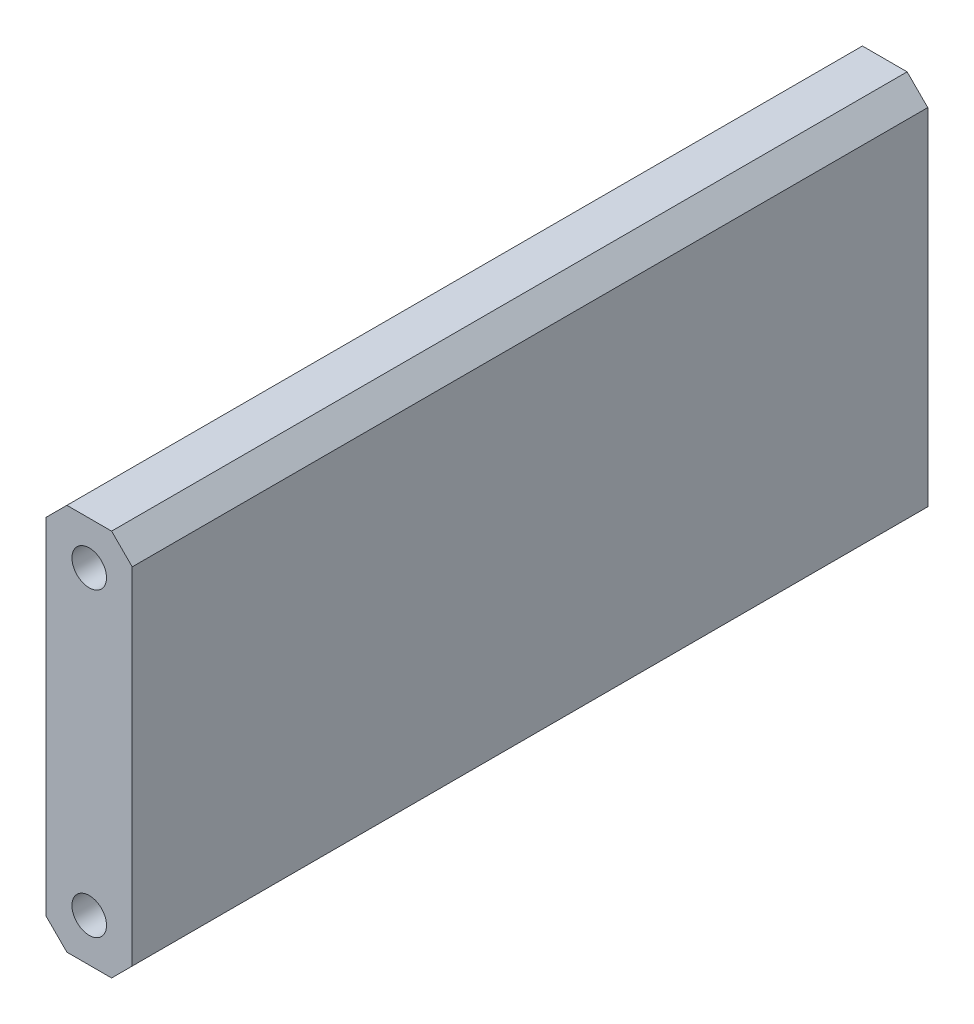
SolidWorks part; units mm, degrees
material "304 SSTL"
ref_plane "Front" through (0, 0, 0) normal (0, 0, 1) x (1, 0, 0)
ref_plane "Top" through (0, 0, 0) normal (0, 1, 0) x (1, 0, 0)
ref_plane "Right" through (0, 0, 0) normal (1, 0, 0) x (0, 0, -1)
sketch "Sketch1" plane through (0, 0, 0) normal (0, 0, 1) x (1, 0, 0)
  line L0 (0, 0) -> (0, -44.45) construction
  line L1 (-3.302, 6.35) -> (-6.35, 3.302)
  line L2 (3.302, 6.35) -> (-3.302, 6.35)
  line L3 (6.35, 3.302) -> (6.35, -47.752)
  line L4 (3.302, -50.8) -> (-3.302, -50.8)
  line L5 (-6.35, 3.302) -> (-6.35, -47.752)
  line L6 (6.35, 3.302) -> (3.302, 6.35)
  line L7 (6.35, -47.752) -> (3.302, -50.8)
  line L8 (-3.302, -50.8) -> (-6.35, -47.752)
  circle A0 centre (0, 0) radius 6.35 construction
  circle A1 centre (0, -44.45) radius 6.35 construction
  point P5 (6.35, 6.35)
  point P6 (-6.35, -50.8)
  point P7 (6.35, -50.8)
  point P8 (-6.35, 6.35)
  dimension "D1" = 12.7
  dimension "D2" = 44.45
  dimension "D5" = 3.048
  dimension "D6" = 3.048
  dimension "D7" = 3.048
  dimension "D8" = 3.048
extrude "Boss-Extrude1" add sketch "Sketch1" along normal blind 117.475
hole_wizard "1/4-20 Tapped Hole1" positions "Sketch3" profile "Sketch2" tap size "1/4-20" standard "Ansi Inch"
sketch "Sketch3" plane through (0, 0, 117.475) normal (0, 0, 1) x (1, 0, 0)
  line L0 (0, 0) -> (0, -44.45) construction
  point P0 (0, 0)
  point P4 (0, -44.45)
  dimension "D1" = 44.45
sketch "Sketch2" plane through (0, 0, 117.475) normal (1, 0, 0) x (0, -1, 0)
  line L0 (0, 0) -> (0, 24.3938)
  line L1 (0, 24.3938) -> (2.5527, 22.86)
  line L2 (2.5527, 22.86) -> (2.5527, 0)
  line L5 (2.5527, 0) -> (0, 0)
  line L10 (0, 24.3938) -> (-2.5527, 22.86) construction
  line L11 (0, -6.35) -> (0, 107.95) construction
  dimension "Tap Drill Dia." = 5.1054
  dimension "Tap Drill Depth" = 22.86
  dimension "Drill Angle" = 118
cosmetic thread "Hole Thread1" parameters "D1"=19.05, "D2"=6.35
cosmetic thread "Hole Thread3" parameters "D1"=19.05, "D2"=6.35
hole_wizard "1/4-20 Tapped Hole2" positions "Sketch5" profile "Sketch4" tap size "1/4-20" standard "Ansi Inch"
sketch "Sketch5" plane through (0, 0, 0) normal (0, 0, -1) x (-1, 0, 0)
  point P0 (0, 0)
  point P4 (0, -44.2439)
sketch "Sketch4" plane through (0, 0, 0) normal (1, 0, 0) x (0, 1, 0)
  line L0 (0, 0) -> (0, 25.4352)
  line L1 (0, 25.4352) -> (2.5527, 23.9014)
  line L2 (2.5527, 23.9014) -> (2.5527, 0)
  line L5 (2.5527, 0) -> (0, 0)
  line L10 (0, 25.4352) -> (-2.5527, 23.9014) construction
  line L11 (0, -6.35) -> (0, 107.95) construction
  dimension "Tap Drill Dia." = 5.1054
  dimension "Tap Drill Depth" = 23.9014
  dimension "Drill Angle" = 118
cosmetic thread "Hole Thread2" parameters "D1"=19.05, "D2"=6.35
cosmetic thread "Hole Thread4" parameters "D1"=19.05, "D2"=6.35
